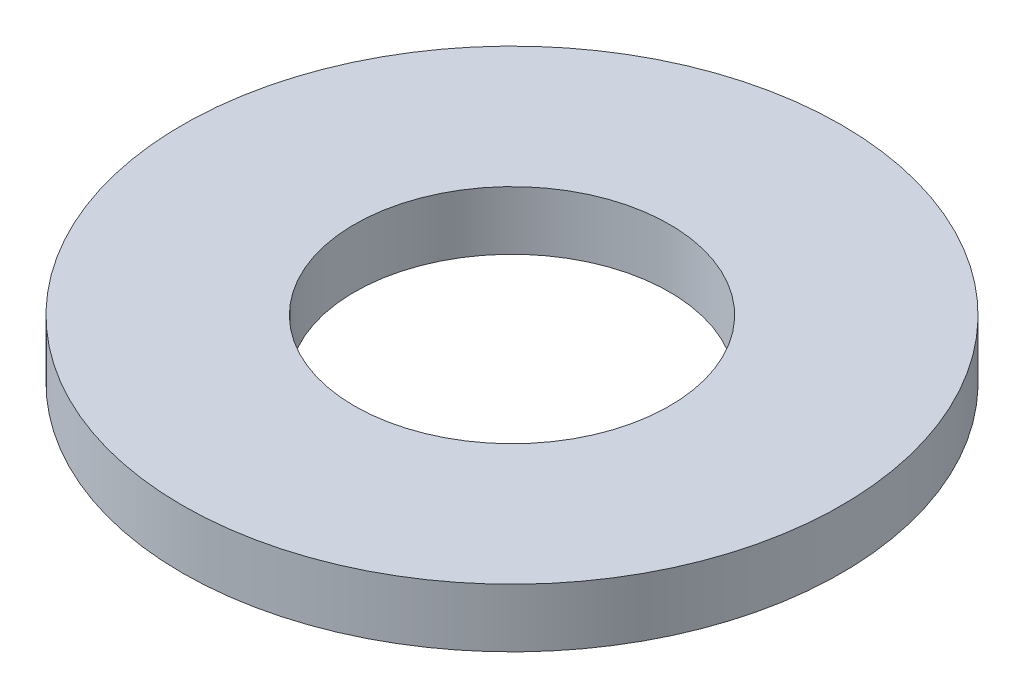
SolidWorks part; units mm, degrees
ref_plane "Front" through (0, 0, 0) normal (0, 0, 1) x (1, 0, 0)
ref_plane "Top" through (0, 0, 0) normal (0, 1, 0) x (1, 0, 0)
ref_plane "Right" through (0, 0, 0) normal (1, 0, 0) x (0, 0, -1)
sketch "Sketch1" plane through (0, 0, 0) normal (0, 1, 0) x (1, 0, 0)
  circle A0 centre (0, 0) radius 2.15
  circle A1 centre (0, 0) radius 4.5
extrude "Extrude1" add sketch "Sketch1" along normal blind 0.8
ref_point "Point1"
